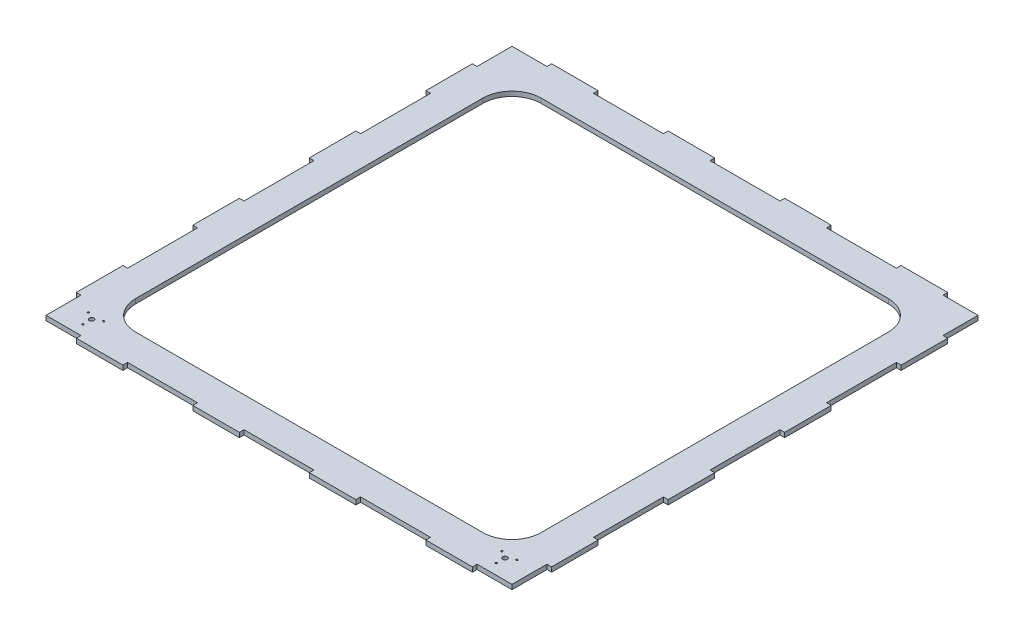
SolidWorks part; units mm, degrees
ref_plane "Front Plane" through (0, 0, 0) normal (0, 0, 1) x (1, 0, 0)
ref_plane "Top Plane" through (0, 0, 0) normal (0, 1, 0) x (1, 0, 0)
ref_plane "Right Plane" through (0, 0, 0) normal (1, 0, 0) x (0, 0, -1)
sketch "Sketch1" plane through (0, 0, 0) normal (0, 1, 0) x (1, 0, 0)
  line L0 (340, 408) -> (260, 408)
  line L1 (400, -400) -> (340, -400)
  line L2 (400, -400) -> (400, -340)
  line L3 (400, 400) -> (340, 400)
  line L4 (-400, -400) -> (-400, -340)
  line L5 (400, -400) -> (-400, 400) construction
  line L6 (400, 400) -> (-400, -400) construction
  line L7 (-408, -340) -> (-408, -260)
  line L8 (340, -408) -> (260, -408)
  line L9 (408, -340) -> (408, -260)
  line L10 (0, 0) -> (0, 601.3427) construction
  line L11 (-200, 601.3427) -> (-200, 42.3001) construction
  line L12 (-300, 493.4621) -> (-300, 335.7003) construction
  line L13 (-340, 408) -> (-340, 400)
  line L14 (-260, 408) -> (-260, 400)
  line L15 (-140, 408) -> (-140, 400)
  line L16 (-60, 408) -> (-60, 400)
  line L17 (60, 408) -> (60, 400)
  line L18 (140, 408) -> (140, 400)
  line L19 (260, 408) -> (260, 400)
  line L20 (340, 408) -> (340, 400)
  line L21 (0, 0) -> (-686.2034, 0) construction
  line L22 (340, -408) -> (340, -400)
  line L23 (260, -408) -> (260, -400)
  line L24 (140, -408) -> (140, -400)
  line L25 (60, -408) -> (60, -400)
  line L26 (-60, -408) -> (-60, -400)
  line L27 (-140, -408) -> (-140, -400)
  line L28 (-260, -408) -> (-260, -400)
  line L29 (-340, -408) -> (-340, -400)
  line L30 (-658.4621, 200) -> (0, 200) construction
  line L31 (-624.1131, 300) -> (-238.3467, 300) construction
  line L32 (-408, 340) -> (-400, 340)
  line L33 (-408, 260) -> (-400, 260)
  line L34 (-408, 140) -> (-400, 140)
  line L35 (-408, 60) -> (-400, 60)
  line L36 (-408, -60) -> (-400, -60)
  line L37 (-408, -140) -> (-400, -140)
  line L38 (-408, -260) -> (-400, -260)
  line L39 (-408, -340) -> (-400, -340)
  line L40 (408, -340) -> (400, -340)
  line L41 (408, -260) -> (400, -260)
  line L42 (408, -140) -> (400, -140)
  line L43 (408, -60) -> (400, -60)
  line L44 (408, 60) -> (400, 60)
  line L45 (408, 140) -> (400, 140)
  line L46 (408, 260) -> (400, 260)
  line L47 (408, 340) -> (400, 340)
  line L48 (-260, 408) -> (-340, 408)
  line L49 (408, 408) -> (-408, 408) construction
  line L50 (-60, 408) -> (-140, 408)
  line L51 (-408, -408) -> (-408, 408) construction
  line L52 (140, 408) -> (60, 408)
  line L53 (408, 260) -> (408, 340)
  line L54 (408, -408) -> (408, 408) construction
  line L55 (408, 60) -> (408, 140)
  line L56 (408, -140) -> (408, -60)
  line L57 (140, -408) -> (60, -408)
  line L58 (408, -408) -> (-408, -408) construction
  line L59 (-60, -408) -> (-140, -408)
  line L60 (-260, -408) -> (-340, -408)
  line L61 (-408, -140) -> (-408, -60)
  line L62 (-408, 60) -> (-408, 140)
  line L63 (-408, 260) -> (-408, 340)
  line L64 (-340, 400) -> (-400, 400)
  line L65 (-140, 400) -> (-260, 400)
  line L66 (400, 400) -> (-400, 400) construction
  line L67 (60, 400) -> (-60, 400)
  line L68 (260, 400) -> (140, 400)
  line L69 (400, 340) -> (400, 400)
  line L70 (400, 140) -> (400, 260)
  line L71 (400, -400) -> (400, 400) construction
  line L72 (400, -60) -> (400, 60)
  line L73 (400, -260) -> (400, -140)
  line L74 (260, -400) -> (140, -400)
  line L75 (60, -400) -> (-60, -400)
  line L76 (400, -400) -> (-400, -400) construction
  line L77 (-140, -400) -> (-260, -400)
  line L78 (-400, -260) -> (-400, -140)
  line L79 (-340, -400) -> (-400, -400)
  line L80 (-400, -400) -> (-400, 400) construction
  line L81 (-400, -60) -> (-400, 60)
  line L82 (-400, 140) -> (-400, 260)
  line L83 (-400, 340) -> (-400, 400)
  point P0 (0, 0)
  dimension "D1" = 800
  dimension "D2" = 800
  dimension "D4" = 200
  dimension "D5" = 100
  dimension "D6" = 40
  dimension "D7" = 200
  dimension "D8" = 100
  dimension "D9" = 40
  dimension "D3" = 8
extrude "Boss-Extrude1" add sketch "Sketch1" along normal blind 8
sketch "Sketch2" plane through (0, 8, 0) normal (0, 1, 0) x (1, 0, 0)
  line L0 (-408, -60) -> (-408, -140) construction
  line L1 (-298, 348) -> (298, 348)
  line L2 (-348, 298) -> (-348, -298)
  line L3 (-298, -348) -> (298, -348)
  line L4 (348, 298) -> (348, -298)
  line L5 (-348, 348) -> (348, -348) construction
  line L6 (-348, -348) -> (348, 348) construction
  line L7 (-140, -408) -> (-60, -408) construction
  arc A0 (-298, 348) -> (-348, 298) centre (-298, 298) ccw
  arc A1 (348, 298) -> (298, 348) centre (298, 298) ccw
  arc A2 (-298, -348) -> (-348, -298) centre (-298, -298) cw
  arc A3 (348, -298) -> (298, -348) centre (298, -298) cw
  point P0 (0, 0)
  point P8 (-408, -100)
  dimension "D3" = 50
  dimension "D1" = 60
  dimension "D2" = 60
extrude "Cut-Extrude1" cut sketch "Sketch2" against normal blind 10
sketch "Sketch3" plane through (0, 8, 0) normal (0, 1, 0) x (1, 0, 0)
  line L1 (260, -408) -> (340, -408) construction
  line L2 (408, -340) -> (408, -260) construction
  line L3 (354.85, -366.85) -> (354.85, -392.8946) construction
  line L4 (0, 0) -> (0, -469.1567) construction
  line L5 (-354.85, -366.85) -> (-354.85, -392.8946) construction
  circle A0 centre (354.85, -366.85) radius 4
  circle A1 centre (354.85, -381.85) radius 1.5
  circle A2 centre (341.8596, -359.35) radius 1.5
  circle A3 centre (367.8404, -359.35) radius 1.5
  circle A4 centre (-367.8404, -359.35) radius 1.5
  circle A5 centre (-341.8596, -359.35) radius 1.5
  circle A6 centre (-354.85, -381.85) radius 1.5
  circle A7 centre (-354.85, -366.85) radius 4
  point P15 (354.85, -366.85)
  dimension "D1" = 8
  dimension "D4" = 3
  dimension "D2" = 41.15
  dimension "D3" = 53.15
  dimension "D5" = 15
  dimension "D6" = 3
extrude "Cut-Extrude2" cut sketch "Sketch3" against normal blind 10
